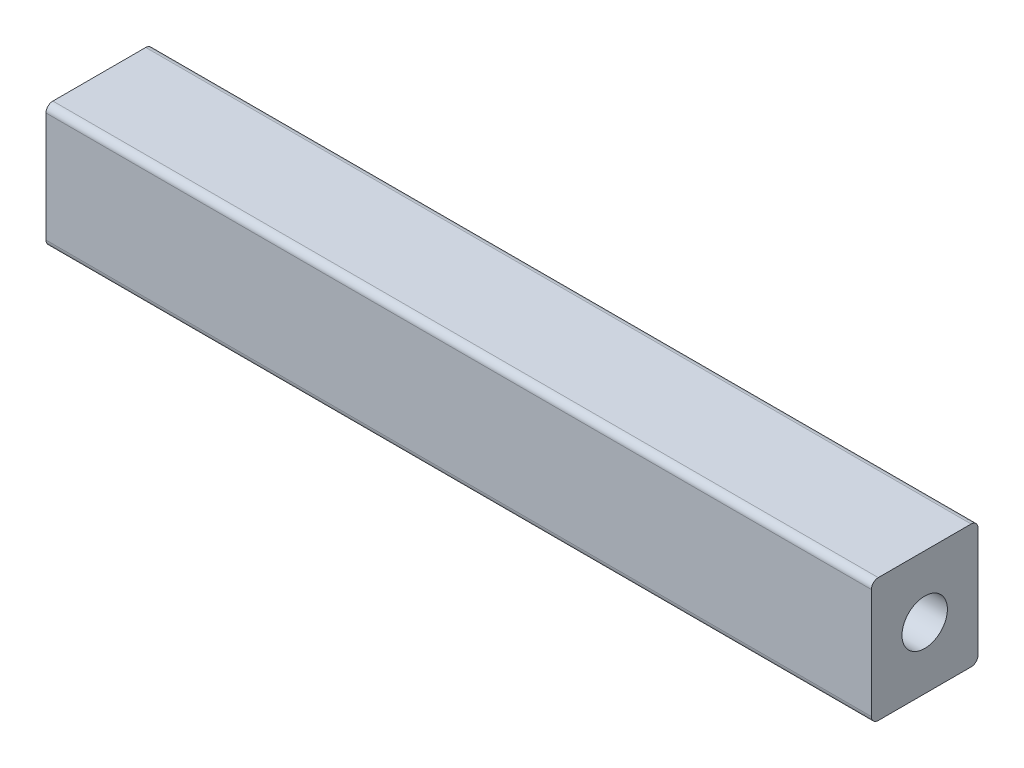
SolidWorks part; units mm, degrees
material "Cedar"
ref_plane "Front Plane" through (0, 0, 0) normal (0, 0, 1) x (1, 0, 0)
ref_plane "Top Plane" through (0, 0, 0) normal (0, 1, 0) x (1, 0, 0)
ref_plane "Right Plane" through (0, 0, 0) normal (1, 0, 0) x (0, 0, -1)
sketch "Sketch1" plane through (0, 0, 0) normal (1, 0, 0) x (0, 0, -1)
  line L1 (-7.75, -9) -> (7.75, -9)
  line L2 (-7.75, -9) -> (-7.75, 9)
  line L3 (-7.75, 9) -> (7.75, 9)
  line L4 (7.75, -9) -> (7.75, 9)
  line L5 (-7.75, -9) -> (7.75, 9) construction
  line L6 (-7.75, 9) -> (7.75, -9) construction
  point P0 (0, 0)
  dimension "D1" = 15.5
  dimension "D2" = 18
extrude "Boss-Extrude1" add sketch "Sketch1" along normal mid plane 120
fillet "Fillet1" radius 1 4 edges at (0, -9, 7.75) (0, -9, -7.75) (0, 9, -7.75) (0, 9, 7.75)
sketch "Sketch4" plane through (60, 0, 0) normal (1, 0, 0) x (0, 0, -1)
  point P0 (0, 0)
hole_wizard "Ø1.0 (6.6) Diameter Hole1" positions "Sketch4" profile "Sketch3" hole size "Ø1.0" standard "ISO"
sketch "Sketch3" plane through (60, 0, 0) normal (0, 1, 0) x (0, 0, -1)
  line L0 (0, 0) -> (0, 13.9828)
  line L1 (0, 13.9828) -> (3.3, 12)
  line L2 (3.3, 12) -> (3.3, 0)
  line L5 (3.3, 0) -> (0, 0)
  line L10 (0, 13.9828) -> (-3.3, 12) construction
  line L11 (0, -6.35) -> (0, 107.95) construction
  dimension "Hole Dia." = 6.6
  dimension "Hole Depth" = 12
  dimension "Drill Angle" = 118
mirror "Mirror1" about plane through (0, 0, 0) normal (1, 0, 0) of "Ø1.0 (6.6) Diameter Hole1"
